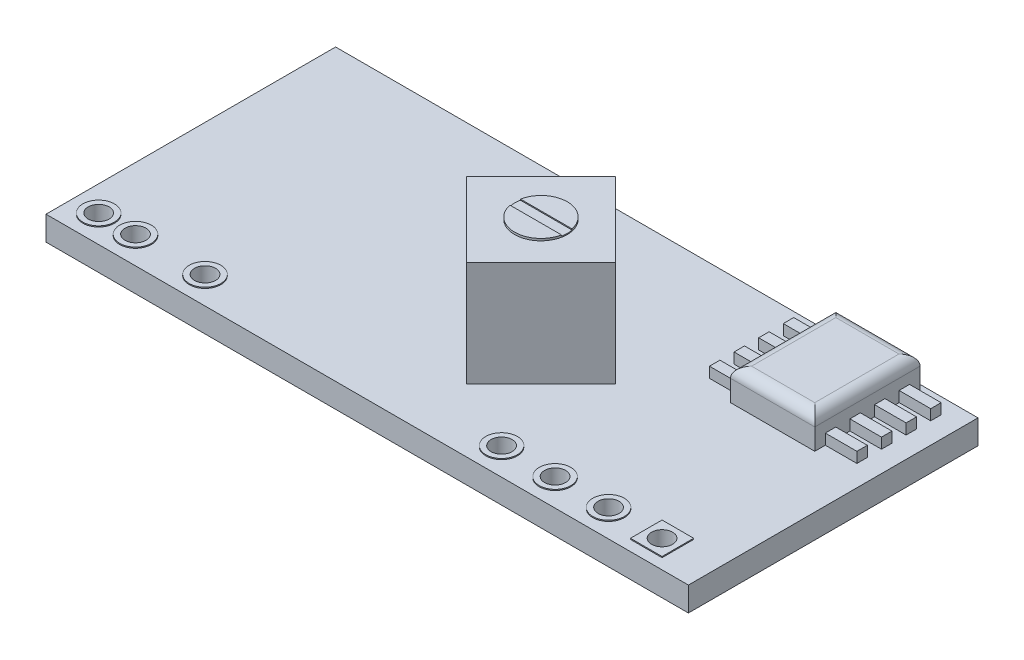
SolidWorks part; units mm, degrees
ref_plane "Front Plane" through (0, 0, 0) normal (0, 0, 1) x (1, 0, 0)
ref_plane "Top Plane" through (0, 0, 0) normal (0, 1, 0) x (1, 0, 0)
ref_plane "Right Plane" through (0, 0, 0) normal (1, 0, 0) x (0, 0, -1)
sketch "Sketch1" plane through (0, 0, 0) normal (0, 1, 0) x (1, 0, 0)
  line L1 (-22.6335, 1.2421) -> (7.8665, 1.2421)
  line L2 (-22.6335, 1.2421) -> (-22.6335, -12.5079)
  line L3 (-22.6335, -12.5079) -> (7.8665, -12.5079)
  line L4 (7.8665, 1.2421) -> (7.8665, -12.5079)
  dimension "D1" = 30.5
  dimension "D2" = 13.75
extrude "Boss-Extrude2" add sketch "Sketch1" along normal blind 1.15
sketch "Sketch3" plane through (0, 1.15, 0) normal (0, 1, 0) x (1, 0, 0)
  line L1 (-9.2046, -5.9724) -> (-5.669, -9.5079)
  line L2 (-5.669, -9.5079) -> (-2.1335, -5.9724)
  line L3 (-2.1335, -5.9724) -> (-5.669, -2.4369)
  line L4 (-5.669, -2.4369) -> (-9.2046, -5.9724)
  line L5 (7.8665, -12.5079) -> (7.8665, 1.2421) construction
  line L6 (-22.6335, -12.5079) -> (7.8665, -12.5079) construction
  dimension "D1" = 5
  dimension "D2" = 5
  dimension "D3" = 10
  dimension "D4" = 3
extrude "Boss-Extrude4" add sketch "Sketch3" along normal blind 5
sketch "Sketch4" plane through (0, 6.15, 0) normal (0, 1, 0) x (1, 0, 0)
  line L2 (-9.2046, -5.9724) -> (-2.1335, -5.9724)
  line L4 (-2.1335, -5.9724) -> (-5.669, -2.4369)
  line L5 (-5.669, -2.4369) -> (-9.2046, -5.9724)
  line L6 (-9.2046, -5.9724) -> (-5.669, -9.5079)
  line L7 (-5.669, -9.5079) -> (-2.1335, -5.9724)
  line L8 (-2.1335, -5.9724) -> (-5.669, -2.4369)
  line L9 (-5.669, -2.4369) -> (-9.2046, -5.9724)
  line L10 (-9.2046, -5.9724) -> (-5.669, -9.5079)
  line L11 (-5.669, -9.5079) -> (-2.1335, -5.9724)
  circle A0 centre (-5.669, -5.9724) radius 1.25
  point P10 (-5.669, -5.9724)
  dimension "D2" = 2.5
  dimension "D1" = 0
extrude "Boss-Extrude5" add sketch "Sketch4" along normal blind 0.1 contours L2 A0 | L2 A0
sketch "Sketch5" plane through (0, 6.25, 0) normal (0, 1, 0) x (1, 0, 0)
  line L0 (-5.669, -9.5079) -> (-2.1335, -5.9724) construction
  line L1 (-9.2046, -5.9724) -> (-5.669, -9.5079) construction
  line L2 (-5.669, -9.5079) -> (-2.1335, -5.9724)
  line L3 (-9.2046, -5.9724) -> (-5.669, -9.5079)
  line L4 (-9.2046, -5.9724) -> (-2.1335, -5.9724)
  line L5 (-6.919, -5.7224) -> (-4.419, -5.7224)
  line L6 (-4.419, -5.7224) -> (-4.419, -6.2224)
  line L7 (-4.419, -6.2224) -> (-6.919, -6.2224)
  line L8 (-6.919, -6.2224) -> (-6.919, -5.7224)
  circle A0 centre (-5.669, -5.9724) radius 1.25 construction
  circle M8 centre (-5.669, -5.9724) radius 1.25
  dimension "D1" = 0.25
  dimension "D2" = 0.25
extrude "Cut-Extrude1" cut sketch "Sketch5" against normal blind 0.05 contours L5 L4 M8 | L7 L4 M8
sketch "Sketch6" plane through (0, 1.15, 0) normal (0, 1, 0) x (1, 0, 0)
  line L0 (7.8665, -12.5079) -> (7.8665, 1.2421) construction
  line L1 (-22.6335, -12.5079) -> (7.8665, -12.5079) construction
  line L2 (7.8665, -12.5079) -> (7.8665, 1.2421)
  line L3 (-22.6335, -12.5079) -> (7.8665, -12.5079)
  line L4 (7.8665, -11.2579) -> (-22.6335, -11.2579)
  line L5 (4.6165, -10.5079) -> (6.1165, -10.5079)
  line L6 (4.6165, -10.5079) -> (4.6165, -12.0079)
  line L7 (4.6165, -12.0079) -> (6.1165, -12.0079)
  line L8 (6.1165, -10.5079) -> (6.1165, -12.0079)
  line L9 (-22.6335, 1.2421) -> (-22.6335, -12.5079) construction
  circle A0 centre (-2.2535, -11.2579) radius 0.75
  circle A1 centre (0.2865, -11.2579) radius 0.75
  circle A2 centre (2.8265, -11.2579) radius 0.75
  circle A3 centre (-19.6335, -11.2579) radius 0.75
  circle A4 centre (-16.3335, -11.2579) radius 0.75
  circle A5 centre (-21.3835, -11.2579) radius 0.75
  point P15 (5.3665, -10.5079)
  dimension "D1" = 1.5
  dimension "D2" = 2.54
  dimension "D3" = 2.54
  dimension "D4" = 2.54
  dimension "D5" = 1.25
  dimension "D6" = 1.75
  dimension "D7" = 3.3
  dimension "D8" = 3
  dimension "D9" = 1.75
extrude "Boss-Extrude6" add sketch "Sketch6" along normal blind 0.05 contours L4 A0 | L4 A0 | L4 A1 | L4 A1 | L4 A2 | L4 A2 | L8 L5 L6 L4 | L8 L4 L6 L7 | L4 A4 | L4 A4 | L4 A3 | L4 A3 | L4 A5 | L4 A5
ref_plane "Plane1" through (0, 0.575, 0) normal (0, 1, 0) x (1, 0, 0)
mirror "Mirror1" about plane through (0, 0.575, 0) normal (0, 1, 0) of "Boss-Extrude6"
sketch "Sketch7" plane through (0, 1.2, 0) normal (0, 1, 0) x (1, 0, 0)
  circle A3 centre (-21.3835, -11.2579) radius 0.5
  circle A4 centre (-19.6335, -11.2579) radius 0.5
  circle A5 centre (-16.3335, -11.2579) radius 0.5
  circle A6 centre (-2.2535, -11.2579) radius 0.5
  circle A7 centre (0.2865, -11.2579) radius 0.5
  circle A8 centre (2.8265, -11.2579) radius 0.5
  circle A9 centre (5.3665, -11.2579) radius 0.5
  dimension "D1" = 1
extrude "Cut-Extrude2" cut sketch "Sketch7" against normal through all
sketch "Sketch8" plane through (0, 1.15, 0) normal (0, 1, 0) x (1, 0, 0)
  line L1 (5.3665, -4.0079) -> (1.3665, -4.0079)
  line L2 (5.3665, -4.0079) -> (5.3665, 0.9921)
  line L3 (5.3665, 0.9921) -> (1.3665, 0.9921)
  line L4 (1.3665, -4.0079) -> (1.3665, 0.9921)
  line L5 (7.8665, 1.2421) -> (-22.6335, 1.2421) construction
  line L6 (7.8665, -12.5079) -> (7.8665, 1.2421) construction
  dimension "D1" = 5
  dimension "D2" = 4
  dimension "D3" = 0.25
  dimension "D4" = 2.5
extrude "Boss-Extrude7" add sketch "Sketch8" along normal blind 1.5
fillet "Fillet1" radius 0.5 4 edges at (3.3665, 2.65, 4.0079) (1.3665, 2.65, 1.5079) (3.3665, 2.65, -0.9921) (5.3665, 2.65, 1.5079)
sketch "Sketch9" plane through (0, 1.15, 0) normal (0, 1, 0) x (1, 0, 0)
  line L0 (5.3665, -4.0079) -> (5.3665, 0.9921) construction
  line L1 (6.8665, -3.5079) -> (5.3665, -3.5079)
  line L2 (6.8665, -3.5079) -> (6.8665, -3.0122)
  line L3 (6.8665, -3.0122) -> (5.3665, -3.0122)
  line L4 (5.3665, -3.5079) -> (5.3665, -3.0122)
  line L5 (1.3665, 0.9921) -> (1.3665, -4.0079) construction
  line L6 (6.8665, -2.3398) -> (5.3665, -2.3398)
  line L7 (6.8665, -2.3398) -> (6.8665, -1.8441)
  line L8 (6.8665, -1.8441) -> (5.3665, -1.8441)
  line L9 (5.3665, -2.3398) -> (5.3665, -1.8441)
  line L10 (6.8665, -1.1717) -> (5.3665, -1.1717)
  line L11 (6.8665, -1.1717) -> (6.8665, -0.676)
  line L12 (6.8665, -0.676) -> (5.3665, -0.676)
  line L13 (5.3665, -1.1717) -> (5.3665, -0.676)
  line L14 (6.8665, -0.0036) -> (5.3665, -0.0036)
  line L15 (6.8665, -0.0036) -> (6.8665, 0.4921)
  line L16 (6.8665, 0.4921) -> (5.3665, 0.4921)
  line L17 (5.3665, -0.0036) -> (5.3665, 0.4921)
  line L18 (-0.1335, -3.5079) -> (1.3665, -3.5079)
  line L19 (-0.1335, -3.5079) -> (-0.1335, -3.0122)
  line L20 (-0.1335, -3.0122) -> (1.3665, -3.0122)
  line L21 (1.3665, -3.5079) -> (1.3665, -3.0122)
  line L23 (-0.1335, -2.3398) -> (1.3665, -2.3398)
  line L24 (-0.1335, -2.3398) -> (-0.1335, -1.8441)
  line L25 (-0.1335, -1.8441) -> (1.3665, -1.8441)
  line L26 (1.3665, -2.3398) -> (1.3665, -1.8441)
  line L27 (-0.1335, -1.1717) -> (1.3665, -1.1717)
  line L28 (-0.1335, -1.1717) -> (-0.1335, -0.676)
  line L29 (-0.1335, -0.676) -> (1.3665, -0.676)
  line L30 (1.3665, -1.1717) -> (1.3665, -0.676)
  line L31 (-0.1335, -0.0036) -> (1.3665, -0.0036)
  line L32 (-0.1335, -0.0036) -> (-0.1335, 0.4921)
  line L33 (-0.1335, 0.4921) -> (1.3665, 0.4921)
  line L34 (1.3665, -0.0036) -> (1.3665, 0.4921)
  line L35 (5.3665, -3.0122) -> (5.3665, -2.3398)
  line L36 (5.3665, -1.8441) -> (5.3665, -1.1717)
  line L37 (5.3665, -0.676) -> (5.3665, -0.0036)
  line L38 (1.3665, -0.0036) -> (1.3665, -0.676)
  line L39 (1.3665, -1.1717) -> (1.3665, -1.8441)
  line L40 (1.3665, -2.3398) -> (1.3665, -3.0122)
  line L42 (1.3665, -4.0079) -> (5.3665, -4.0079) construction
  line M58 (5.3665, 0.9921) -> (5.3665, -4.0079)
  line M60 (1.3665, -4.0079) -> (1.3665, 0.9921)
  dimension "D1" = 1.5
  dimension "D2" = 0.4957
  dimension "D3" = 0.5
  dimension "D4" = 4
  dimension "D5" = 0.5
extrude "Boss-Extrude8" add sketch "Sketch9" along normal blind 0.5 contours L11 L12 L10 M58 | L7 L8 L6 M58 | L2 L3 L1 M58 | L15 L16 L14 M58 | L20 L19 L18 M60 | L25 L24 L23 M60 | L29 L28 L27 M60 | L33 L32 L31 M60
equation "\"D3@Sketch6\"=\"D2@Sketch6\""
equation "\"D4@Sketch6\"=\"D2@Sketch6\""
